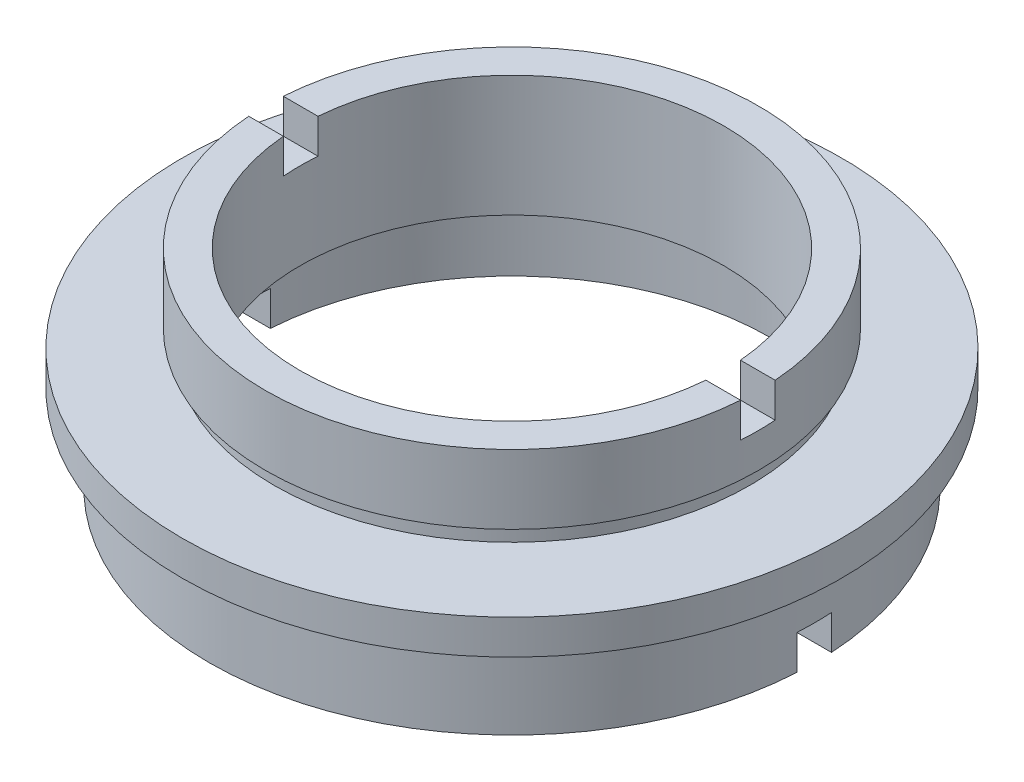
SolidWorks part; units mm, degrees
ref_plane "前视基准面" through (0, 0, 0) normal (0, 0, 1) x (1, 0, 0)
ref_plane "上视基准面" through (0, 0, 0) normal (0, 1, 0) x (1, 0, 0)
ref_plane "右视基准面" through (0, 0, 0) normal (1, 0, 0) x (0, 0, -1)
sketch "草图1" plane through (0, 0, 0) normal (0, 0, 1) x (1, 0, 0)
  line L0 (0, 22.6775) -> (0, 0) construction
  line L1 (-12.25, 12) -> (-14.25, 12)
  line L2 (-14.25, 12) -> (-14.25, 8)
  line L3 (-14.25, 8) -> (-13.75, 8)
  line L4 (-13.75, 8) -> (-13.75, 7)
  line L5 (-13.75, 7) -> (-19.05, 7)
  line L6 (-19.05, 7) -> (-19.05, 5)
  line L7 (-19.05, 5) -> (-17, 5)
  line L8 (-17, 5) -> (-17, 4)
  line L9 (-17, 4) -> (-17.5, 4)
  line L10 (-17.5, 4) -> (-17.5, 0)
  line L11 (-17.5, 0) -> (-15, 0)
  line L12 (-15, 0) -> (-15, 4)
  line L13 (-12.25, 5) -> (-15.6, 5)
  line L14 (-15.6, 5) -> (-15.6, 4)
  line L15 (-15.6, 4) -> (-15, 4)
  line L16 (-12.25, 12) -> (-12.25, 5)
  point P3 (-15.3, 4)
  point P5 (-19.05, 6)
  dimension "D2" = 1
  dimension "D3" = 1
  dimension "D4" = 5
  dimension "D5" = 5
  dimension "D6" = 14.25
  dimension "D7" = 19.05
  dimension "D8" = 17.5
  dimension "D9" = 17
  dimension "D10" = 13.75
  dimension "D11" = 15
  dimension "D12" = 0
  dimension "D13" = 15.6
  dimension "D14" = 12.25
  dimension "D15" = 12
  dimension "D16" = 7
  dimension "D17" = 1
revolve "旋转1" add sketch "草图1" angle 360 about L0
cosmetic thread "装饰螺纹线1" parameters "D2"=27.5
cosmetic thread "装饰螺纹线2" parameters "D2"=34
cosmetic thread "装饰螺纹线3" parameters "D2"=31
cosmetic thread "装饰螺纹线4" parameters "D2"=25.5
sketch "草图2" plane through (0, 0, 0) normal (1, 0, 0) x (0, 0, -1)
  line L0 (15, 12) -> (-15, 12) construction
  line L1 (-1, 13.594) -> (1, 13.594)
  line L2 (-1, 13.594) -> (-1, 10)
  line L3 (-1, 10) -> (1, 10)
  line L4 (1, 13.594) -> (1, 10)
  line L5 (-1, 2) -> (1, 2)
  line L6 (-1, 2) -> (-1, -4.6679)
  line L7 (-1, -4.6679) -> (1, -4.6679)
  line L8 (1, 2) -> (1, -4.6679)
  dimension "D1" = 2
  dimension "D2" = 1
  dimension "D3" = 2
  dimension "D4" = 1
  dimension "D5" = 2
  dimension "D6" = 2
extrude "切除-拉伸1" cut sketch "草图2" against normal mid plane 79
